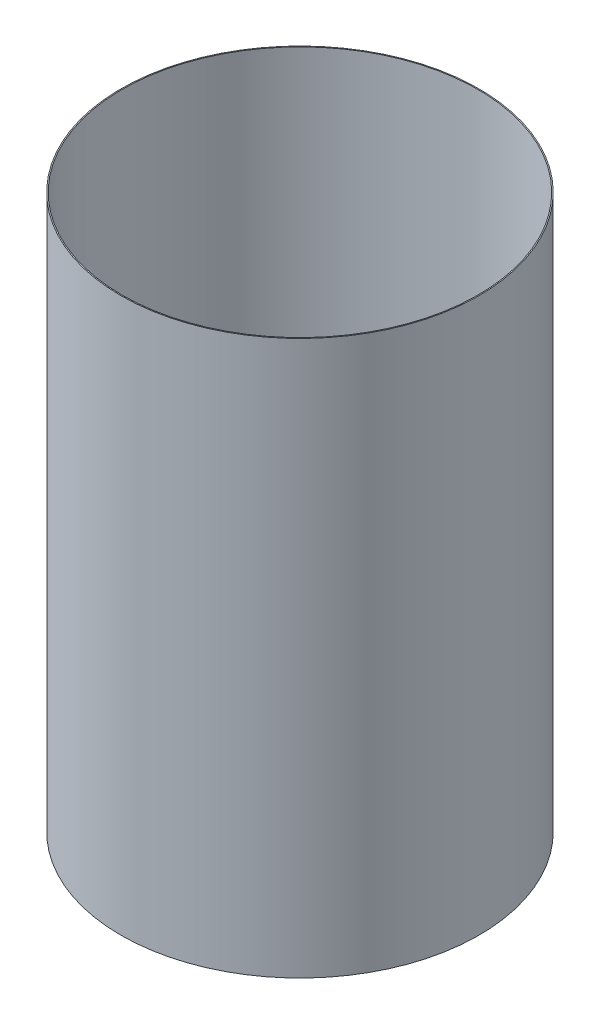
SolidWorks part; units mm, degrees
material "Thornel Mat VMA"
ref_plane "Front Plane" through (0, 0, 0) normal (0, 0, 1) x (1, 0, 0)
ref_plane "Top Plane" through (0, 0, 0) normal (0, 1, 0) x (1, 0, 0)
ref_plane "Right Plane" through (0, 0, 0) normal (1, 0, 0) x (0, 0, -1)
ref_axis "Axis1" through (0, 55, 0) along (0, -1, 0)
sketch "Sketch1" plane through (0, 0, 0) normal (0, 0, 1) x (1, 0, 0)
  line L0 (-42.8625, -69.0032) -> (-42.8625, -202.3532)
  line L2 (-38.1, -202.3532) -> (0, -202.3532) construction
  line L3 (-38.1, -69.0032) -> (0, -69.0032) construction
revolve "Revolve-Thin1" add sketch "Sketch1" angle 360 about axis through (0, 55, 0) along (0, -1, 0)
equation "\"D3@Revolve-Thin1\"=\"CF THICKNESS@Cryo Tank.Assembly\""
